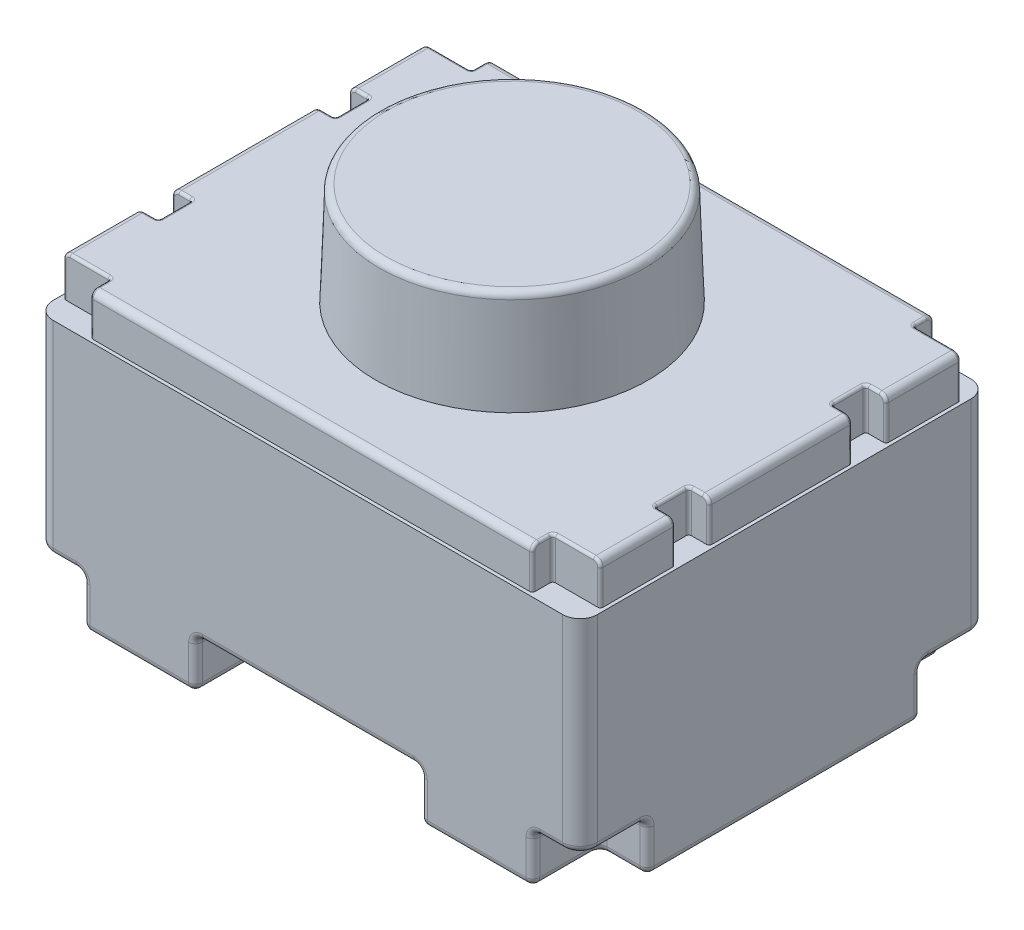
SolidWorks part; units mm, degrees
ref_plane "Front Plane" through (0, 0, 0) normal (0, 0, 1) x (1, 0, 0)
ref_plane "Top Plane" through (0, 0, 0) normal (0, 1, 0) x (1, 0, 0)
ref_plane "Right Plane" through (0, 0, 0) normal (1, 0, 0) x (0, 0, -1)
sketch "Sketch1" plane through (0, 0, 0) normal (0, 1, 0) x (1, 0, 0)
  line L1 (-2, -1.5) -> (2, -1.5)
  line L2 (-2, -1.5) -> (-2, 1.5)
  line L3 (-2, 1.5) -> (2, 1.5)
  line L4 (2, -1.5) -> (2, 1.5)
  line L5 (-2, -1.5) -> (2, 1.5) construction
  line L6 (-2, 1.5) -> (2, -1.5) construction
  point P0 (0, 0)
  dimension "D1" = 4
  dimension "D2" = 3
extrude "Boss-Extrude1" add sketch "Sketch1" along normal blind 1.5 from offset 0.5588
fillet "Fillet1" radius 0.127 4 edges at (-2, 1.3088, 1.5) (-2, 1.3088, -1.5) (2, 1.3088, -1.5) (2, 1.3088, 1.5)
sketch "Sketch2" plane through (0, 2.0588, 0) normal (0, -1, 0) x (-1, 0, 0)
  line L8 (1.9746, -1.373) -> (1.9746, 1.373)
  line L9 (-1.873, -1.4746) -> (1.873, -1.4746)
  line L10 (-1.9746, 1.373) -> (-1.9746, -1.373)
  line L11 (1.873, 1.4746) -> (-1.873, 1.4746)
  line L12 (1.9746, -1.373) -> (1.9746, 1.373)
  line L13 (-1.873, -1.4746) -> (1.873, -1.4746)
  line L14 (-1.9746, 1.373) -> (-1.9746, -1.373)
  line L15 (1.873, 1.4746) -> (-1.873, 1.4746)
  arc A8 (1.873, -1.4746) -> (1.9746, -1.373) centre (1.873, -1.373) ccw
  arc A9 (-1.9746, -1.373) -> (-1.873, -1.4746) centre (-1.873, -1.373) ccw
  arc A10 (-1.873, 1.4746) -> (-1.9746, 1.373) centre (-1.873, 1.373) ccw
  arc A11 (1.9746, 1.373) -> (1.873, 1.4746) centre (1.873, 1.373) ccw
  arc A12 (1.873, -1.4746) -> (1.9746, -1.373) centre (1.873, -1.373) ccw
  arc A13 (-1.9746, -1.373) -> (-1.873, -1.4746) centre (-1.873, -1.373) ccw
  arc A14 (-1.873, 1.4746) -> (-1.9746, 1.373) centre (-1.873, 1.373) ccw
  arc A15 (1.9746, 1.373) -> (1.873, 1.4746) centre (1.873, 1.373) ccw
  dimension "D1" = 0.0254
extrude "Boss-Extrude2" add sketch "Sketch2" against normal blind 0.3048
sketch "Sketch3" plane through (0, 0, 0) normal (0, 1, 0) x (1, 0, 0)
  line L0 (-1.6532, -1.5) -> (-1.6532, -1.0069)
  line L1 (-1.873, -1.5) -> (1.873, -1.5) construction
  line L2 (-1.6532, -1.0069) -> (-2, -1.0069)
  line L3 (-2, 1.373) -> (-2, -1.373) construction
  line L4 (-1.5828, -0.4738) -> (-0.8264, -0.4738)
  line L5 (-0.8264, -0.4738) -> (-0.8264, -1.5)
  line L6 (-1.5828, -0.4738) -> (-1.5828, 0.4738)
  line L7 (-1.6532, -1.5) -> (-0.8264, -1.5)
  line L8 (-2, -1.0069) -> (-2, 1.0069)
  line L9 (-1.5828, 0) -> (-2, 0) construction
  line L10 (-1.6532, 1.5) -> (-0.8264, 1.5)
  line L11 (-0.8264, 0.4738) -> (-0.8264, 1.5)
  line L12 (-1.5828, 0.4738) -> (-0.8264, 0.4738)
  line L13 (-1.6532, 1.0069) -> (-2, 1.0069)
  line L14 (-1.6532, 1.5) -> (-1.6532, 1.0069)
  line L15 (0, -1.5) -> (0, 1.5) construction
  line L16 (1.873, 1.5) -> (-1.873, 1.5) construction
  line L17 (1.5828, 0) -> (2, 0) construction
  line L18 (1.6532, 1.5) -> (1.6532, 1.0069)
  line L19 (1.6532, 1.0069) -> (2, 1.0069)
  line L20 (1.5828, 0.4738) -> (0.8264, 0.4738)
  line L21 (0.8264, 0.4738) -> (0.8264, 1.5)
  line L22 (1.6532, 1.5) -> (0.8264, 1.5)
  line L23 (2, -1.0069) -> (2, 1.0069)
  line L24 (1.6532, -1.5) -> (0.8264, -1.5)
  line L25 (1.5828, -0.4738) -> (1.5828, 0.4738)
  line L26 (0.8264, -0.4738) -> (0.8264, -1.5)
  line L27 (1.5828, -0.4738) -> (0.8264, -0.4738)
  line L28 (1.6532, -1.0069) -> (2, -1.0069)
  line L29 (1.6532, -1.5) -> (1.6532, -1.0069)
  dimension "D1" = 3
  dimension "D2" = 4
extrude "Boss-Extrude3" add sketch "Sketch3" along normal up to next from offset 0.2
sketch "Sketch5" plane through (0, 2.3636, 0) normal (0, 1, 0) x (1, 0, 0)
  circle A0 centre (0, 0) radius 1
  dimension "D1" = 2
extrude "Boss-Extrude5" add sketch "Sketch5" along normal blind 0.75 draft 2
fillet "Fillet3" radius 0.0508 88 edges at (1.9628, 0.5588, 1.4628) (1.9628, 0.5588, -1.4628) (-1.9628, 0.5588, -1.4628) (-1.9628, 0.5588, 1.4628) (2, 0.5588, 1.19) (2, 0.5588, -1.19) (0.8264, 0.3794, 1.5) (0.8264, 0.3794, -1.5) (1.9448, 2.3636, -1.4448) (0, 2.3636, -1.4746) (-1.9448, 2.3636, -1.4448) (-1.9746, 2.3636, 0) (-1.9448, 2.3636, 1.4448) (0, 2.3636, 1.4746) (1.9448, 2.3636, 1.4448) (1.5828, 0.3794, 0.4738) (0.8264, 0.3794, 0.4738) (0.8264, 0.3794, -0.4738) (1.5828, 0.3794, -0.4738) (-0.8264, 0.3794, 0.4738) (-1.5828, 0.3794, 0.4738) (-1.5828, 0.3794, -0.4738) (-0.8264, 0.3794, -0.4738) (1.8266, 0.5588, 1.0069) (2, 0.3794, 1.0069) (1.6532, 0.3794, 1.5) (1.6532, 0.5588, 1.2535) (1.6532, 0.3794, 1.0069) (2, 0.3794, -1.0069) (1.8266, 0.5588, -1.0069) (1.6532, 0.3794, -1.0069) (1.6532, 0.5588, -1.2535) (1.6532, 0.3794, -1.5) (-1.6532, 0.3794, -1.0069) (-1.6532, 0.3794, 1.0069) (-1.2046, 0.5588, -0.4738) (-1.5828, 0.5588, 0) (-1.2046, 0.5588, 0.4738) (0.8264, 0.5588, 0.9869) (1.2046, 0.5588, 0.4738) (1.5828, 0.5588, 0) (1.2046, 0.5588, -0.4738) (0.8264, 0.5588, -0.9869) (-0.8264, 0.2, 0.9869) (-1.2046, 0.2, 0.4738) (-1.5828, 0.2, 0) (-1.2046, 0.2, -0.4738) (-0.8264, 0.2, -0.9869) (-1.2398, 0.2, -1.5) (-1.6532, 0.2, -1.2535) (-1.8266, 0.2, -1.0069) (-2, 0.2, 0) (-1.8266, 0.2, 1.0069) (-1.6532, 0.2, 1.2535) (-1.2398, 0.2, 1.5) (0.8264, 0.2, -0.9869) (1.2046, 0.2, -0.4738) (1.5828, 0.2, 0) (1.2046, 0.2, 0.4738) (0.8264, 0.2, 0.9869) (1.2398, 0.2, 1.5) (1.6532, 0.2, 1.2535) (1.8266, 0.2, 1.0069) (2, 0.2, 0) (1.8266, 0.2, -1.0069) (1.6532, 0.2, -1.2535) (1.2398, 0.2, -1.5) (1.9746, 2.3636, 0)
sketch "Sketch6" plane through (0, 2.3636, 0) normal (0, 1, 0) x (1, 0, 0)
  line L0 (-1.9746, -1.373) -> (-1.9746, 1.373) construction
  line L1 (-1.9746, 0.775) -> (-1.8246, 0.775)
  line L2 (-1.9746, 0.775) -> (-1.9746, 0.525)
  line L3 (-1.9746, 0.525) -> (-1.8246, 0.525)
  line L4 (-1.8246, 0.775) -> (-1.8246, 0.525)
  line L5 (-1.9746, 0.775) -> (-1.8246, 0.525) construction
  line L6 (-1.9746, 0.525) -> (-1.8246, 0.775) construction
  line L7 (0, 0) -> (0, 2.2745) construction
  line L8 (-1.6246, 1.3246) -> (-1.9746, 1.3246)
  line L9 (-1.6246, 1.3246) -> (-1.6246, 1.4746)
  line L10 (-1.6246, 1.4746) -> (-1.873, 1.4746)
  line L11 (-1.9746, 1.3246) -> (-1.9746, 1.373)
  line L12 (-1.6246, 1.3246) -> (-1.8858, 1.4738) construction
  line L13 (-1.6246, 1.4746) -> (-1.9746, 1.3246) construction
  line L14 (0, 0) -> (-4.562, 0) construction
  line L15 (1.6246, 1.4746) -> (1.9746, 1.3246) construction
  line L16 (1.6246, 1.3246) -> (1.8858, 1.4738) construction
  line L17 (1.9746, 0.525) -> (1.8246, 0.775) construction
  line L18 (1.9746, 0.775) -> (1.8246, 0.525) construction
  line L19 (1.9746, 1.3246) -> (1.9746, 1.373)
  line L20 (1.6246, 1.4746) -> (1.873, 1.4746)
  line L21 (1.6246, 1.3246) -> (1.6246, 1.4746)
  line L22 (1.6246, 1.3246) -> (1.9746, 1.3246)
  line L23 (1.8246, 0.775) -> (1.8246, 0.525)
  line L24 (1.9746, 0.525) -> (1.8246, 0.525)
  line L25 (1.9746, 0.775) -> (1.9746, 0.525)
  line L26 (1.9746, 0.775) -> (1.8246, 0.775)
  line L27 (1.9746, -0.775) -> (1.8246, -0.525) construction
  line L28 (1.9746, -0.525) -> (1.8246, -0.775) construction
  line L29 (1.6246, -1.3246) -> (1.8858, -1.4738) construction
  line L30 (1.6246, -1.4746) -> (1.9746, -1.3246) construction
  line L31 (-1.6246, -1.4746) -> (-1.9746, -1.3246) construction
  line L32 (-1.6246, -1.3246) -> (-1.8858, -1.4738) construction
  line L33 (-1.9746, -0.525) -> (-1.8246, -0.775) construction
  line L34 (-1.9746, -0.775) -> (-1.8246, -0.525) construction
  line L35 (1.9746, -0.775) -> (1.8246, -0.775)
  line L36 (1.9746, -0.775) -> (1.9746, -0.525)
  line L37 (1.9746, -0.525) -> (1.8246, -0.525)
  line L38 (1.8246, -0.775) -> (1.8246, -0.525)
  line L39 (1.6246, -1.3246) -> (1.9746, -1.3246)
  line L40 (1.6246, -1.3246) -> (1.6246, -1.4746)
  line L41 (1.6246, -1.4746) -> (1.873, -1.4746)
  line L42 (1.9746, -1.3246) -> (1.9746, -1.373)
  line L43 (-1.9746, -1.3246) -> (-1.9746, -1.373)
  line L44 (-1.6246, -1.4746) -> (-1.873, -1.4746)
  line L45 (-1.6246, -1.3246) -> (-1.6246, -1.4746)
  line L46 (-1.6246, -1.3246) -> (-1.9746, -1.3246)
  line L47 (-1.8246, -0.775) -> (-1.8246, -0.525)
  line L48 (-1.9746, -0.525) -> (-1.8246, -0.525)
  line L49 (-1.9746, -0.775) -> (-1.9746, -0.525)
  line L50 (-1.9746, -0.775) -> (-1.8246, -0.775)
  arc A0 (-1.873, 1.4746) -> (-1.9746, 1.373) centre (-1.873, 1.373) ccw construction
  arc A1 (-1.873, 1.4746) -> (-1.9746, 1.373) centre (-1.873, 1.373) ccw
  arc A2 (1.873, 1.4746) -> (1.9746, 1.373) centre (1.873, 1.373) cw
  arc A3 (1.873, -1.4746) -> (1.9746, -1.373) centre (1.873, -1.373) ccw
  arc A4 (-1.873, -1.4746) -> (-1.9746, -1.373) centre (-1.873, -1.373) cw
  point P4 (-1.8996, 0.65)
  point P14 (-1.7747, 1.4103)
  point P30 (1.7747, 1.4103)
  point P31 (1.8996, 0.65)
  point P54 (1.8996, -0.65)
  point P55 (1.7747, -1.4103)
  point P56 (-1.7747, -1.4103)
  point P57 (-1.8996, -0.65)
  dimension "D1" = 0.65
  dimension "D2" = 0.25
  dimension "D3" = 0.15
  dimension "D4" = 0.15
  dimension "D5" = 0.35
extrude "Cut-Extrude1" cut sketch "Sketch6" against normal up to surface (0.3048 mm away) up to face at (0, 2.0588, 0)
fillet "Fillet4" radius 0.02 62 edges at (-1.6246, 2.2112, 1.3246) (-1.6246, 2.1858, 1.4746) (-1.6246, 2.3487, 1.4597) (-1.6246, 2.3636, 1.3742) (-1.7742, 2.3636, 1.3246) (-1.9597, 2.3487, 1.3246) (-1.9746, 2.1858, 1.3246) (-1.9746, 2.1858, 0.525) (-1.9597, 2.3487, 0.525) (-1.8742, 2.3636, 0.525) (-1.8246, 2.2112, 0.525) (-1.8246, 2.3636, 0.65) (-1.8246, 2.2112, 0.775) (-1.8742, 2.3636, 0.775) (-1.9597, 2.3487, 0.775) (-1.9746, 2.1858, 0.775) (-1.9746, 2.1858, -0.525) (-1.9597, 2.3487, -0.525) (-1.8742, 2.3636, -0.525) (-1.8246, 2.2112, -0.525) (-1.8246, 2.3636, -0.65) (-1.8246, 2.2112, -0.775) (-1.8742, 2.3636, -0.775) (-1.9597, 2.3487, -0.775) (-1.9746, 2.1858, -0.775) (-1.9746, 2.1858, -1.3246) (-1.9597, 2.3487, -1.3246) (-1.7742, 2.3636, -1.3246) (-1.6246, 2.2112, -1.3246) (-1.6246, 2.3636, -1.3742) (-1.6246, 2.3487, -1.4597) (-1.6246, 2.1858, -1.4746) (1.6246, 2.1858, -1.4746) (1.6246, 2.3487, -1.4597) (1.6246, 2.3636, -1.3742) (1.9746, 2.1858, -1.3246) (1.9597, 2.3487, -1.3246) (1.7742, 2.3636, -1.3246) (1.6246, 2.2112, -1.3246) (1.8246, 2.2112, -0.775) (1.9746, 2.1858, -0.775) (1.9597, 2.3487, -0.775) (1.8742, 2.3636, -0.775) (1.8246, 2.3636, -0.65) (1.9746, 2.1858, -0.525) (1.8742, 2.3636, -0.525) (1.9597, 2.3487, -0.525) (1.8246, 2.2112, -0.525) (1.9746, 2.1858, 0.525) (1.8742, 2.3636, 0.525) (1.9597, 2.3487, 0.525) (1.8246, 2.2112, 0.525) (1.8246, 2.3636, 0.65) (1.9746, 2.1858, 1.3246) (1.6246, 2.1858, 1.4746) (1.9597, 2.3487, 0.775) (1.8742, 2.3636, 0.775) (1.8246, 2.2112, 0.775) (1.9746, 2.1858, 0.775) (1.6246, 2.2112, 1.3246) (1.6246, 2.3636, 1.3742) (1.7742, 2.3636, 1.3246)
fillet "Fillet5" radius 0.05 1 edges at (0, 3.1136, 0.9738)
